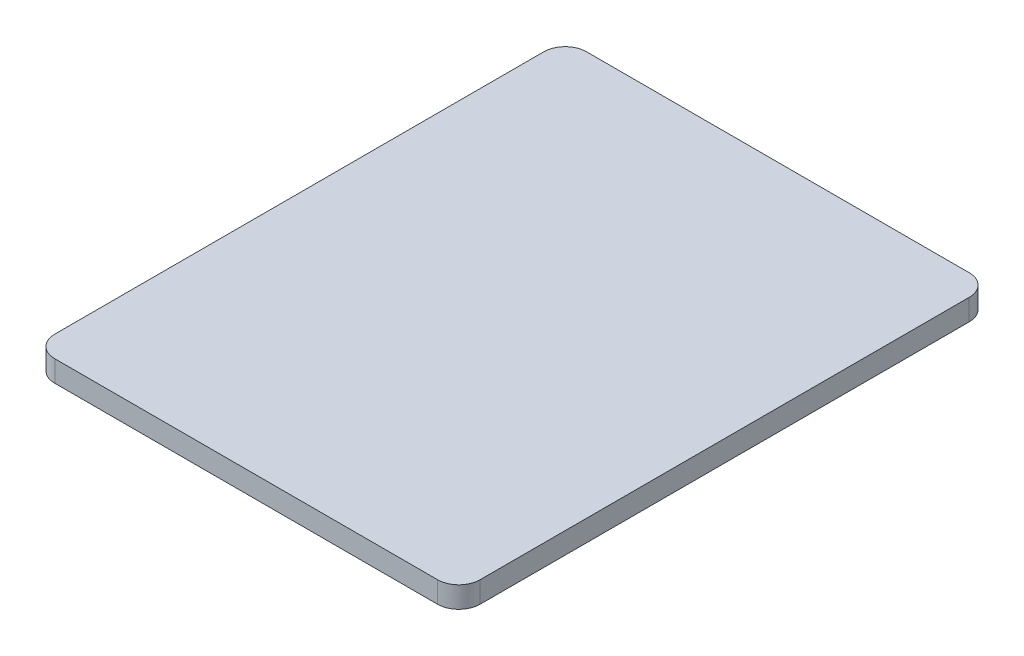
SolidWorks part; units mm, degrees
ref_plane "Front Plane" through (0, 0, 0) normal (0, 0, 1) x (1, 0, 0)
ref_plane "Top Plane" through (0, 0, 0) normal (0, 1, 0) x (1, 0, 0)
ref_plane "Right Plane" through (0, 0, 0) normal (1, 0, 0) x (0, 0, -1)
sketch "Sketch1" plane through (0, 0, 0) normal (0, 1, 0) x (1, 0, 0)
  line L1 (-100, -125) -> (100, -125)
  line L2 (-100, -125) -> (-100, 125)
  line L3 (-100, 125) -> (100, 125)
  line L4 (100, -125) -> (100, 125)
  line L5 (-100, -125) -> (100, 125) construction
  line L6 (-100, 125) -> (100, -125) construction
  point P0 (0, 0)
  dimension "D1" = 200
  dimension "D2" = 250
extrude "Boss-Extrude1" add sketch "Sketch1" along normal blind 10
fillet "Fillet1" radius 10 2 edges at (100, 5, -125) (100, 5, 125)
fillet "Fillet2" radius 10 2 edges at (-100, 5, -125) (-100, 5, 125)
